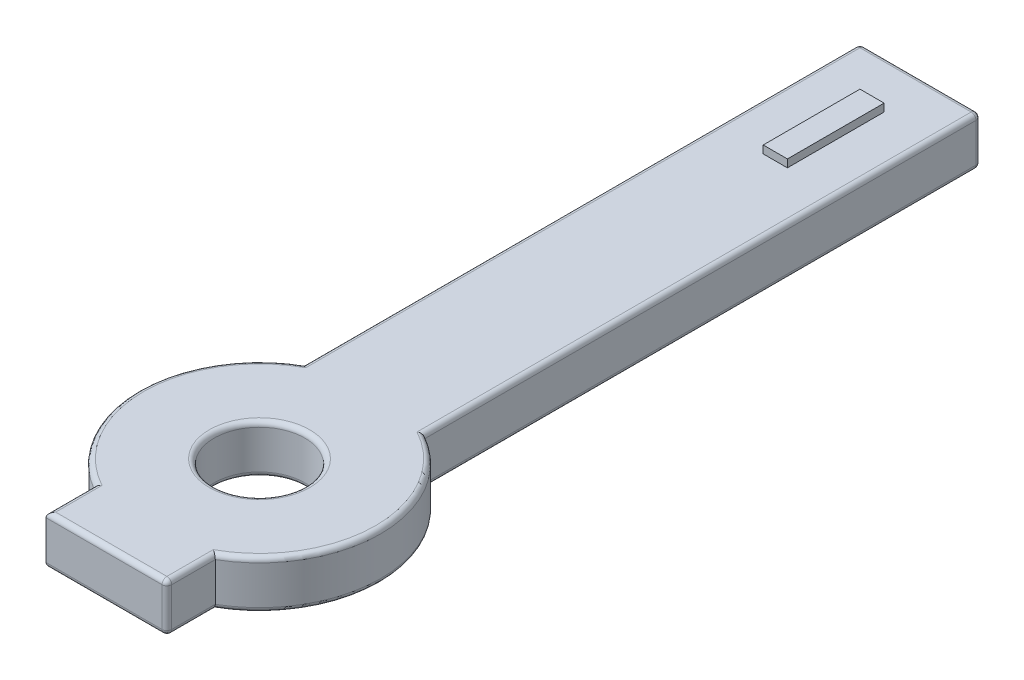
SolidWorks part; units mm, degrees
ref_plane "前视基准面" through (0, 0, 0) normal (0, 0, 1) x (1, 0, 0)
ref_plane "上视基准面" through (0, 0, 0) normal (0, 1, 0) x (1, 0, 0)
ref_plane "右视基准面" through (0, 0, 0) normal (1, 0, 0) x (0, 0, -1)
other "Configuration Table"
sketch "草图1" plane through (0, 0, 0) normal (0, 1, 0) x (1, 0, 0)
  line L0 (-2.5, 27.3301) -> (-2.5, 4.3301)
  line L1 (-2.5, 27.3301) -> (2.5, 27.3301)
  line L2 (2.5, 27.3301) -> (2.5, 4.3301)
  line L3 (0, 0) -> (0, 11.485) construction
  line L4 (-2.5, -4.3301) -> (-2.5, -6.3301)
  line L5 (-2.5, -6.3301) -> (2.5, -6.3301)
  line L6 (2.5, -6.3301) -> (2.5, -4.3301)
  circle A0 centre (0, 0) radius 1.875
  circle A1 centre (0, 0) radius 5
  dimension "D1" = 3.75
  dimension "D2" = 10
  dimension "D3" = 23
  dimension "D4" = 5
  dimension "D5" = 2
extrude "凸台-拉伸1" add sketch "草图1" along normal blind 2
fillet "圆角1" radius 0.2 21 edges at (0, 2, 1.875) (0, 0, 1.875) (2.5, 0, -15.8301) (2.5, 2, -15.8301) (0, 0, -27.3301) (0, 2, -27.3301) (-2.5, 0, -15.8301) (-2.5, 2, -15.8301) (-5, 0, 0) (-5, 2, 0) (-2.5, 0, 5.3301) (-2.5, 2, 5.3301) (0, 0, 6.3301) (0, 2, 6.3301) (2.5, 0, 5.3301) (2.5, 2, 5.3301) (5, 0, 0) (5, 2, 0) (2.5, 1, 6.3301) (-2.5, 1, -27.3301) (2.5, 1, -27.3301)
sketch "草图2" plane through (0, 2, 0) normal (0, 1, 0) x (1, 0, 0)
  line L0 (-2.5, 27.3301) -> (2.5, 27.3301) construction
  line L1 (-0.5, 25.3301) -> (0.5, 25.3301)
  line L2 (-0.5, 25.3301) -> (-0.5, 21.3301)
  line L3 (-0.5, 21.3301) -> (0.5, 21.3301)
  line L4 (0.5, 25.3301) -> (0.5, 21.3301)
  line L5 (2.5, 27.3301) -> (2.5, 4.3301) construction
  line L6 (-2.5, 27.3301) -> (-2.5, -4.3301) construction
  dimension "D1" = 2
  dimension "D2" = 2
  dimension "D3" = 2
  dimension "D4" = 4
extrude "凸台-拉伸2" add sketch "草图2" along normal blind 0.32
